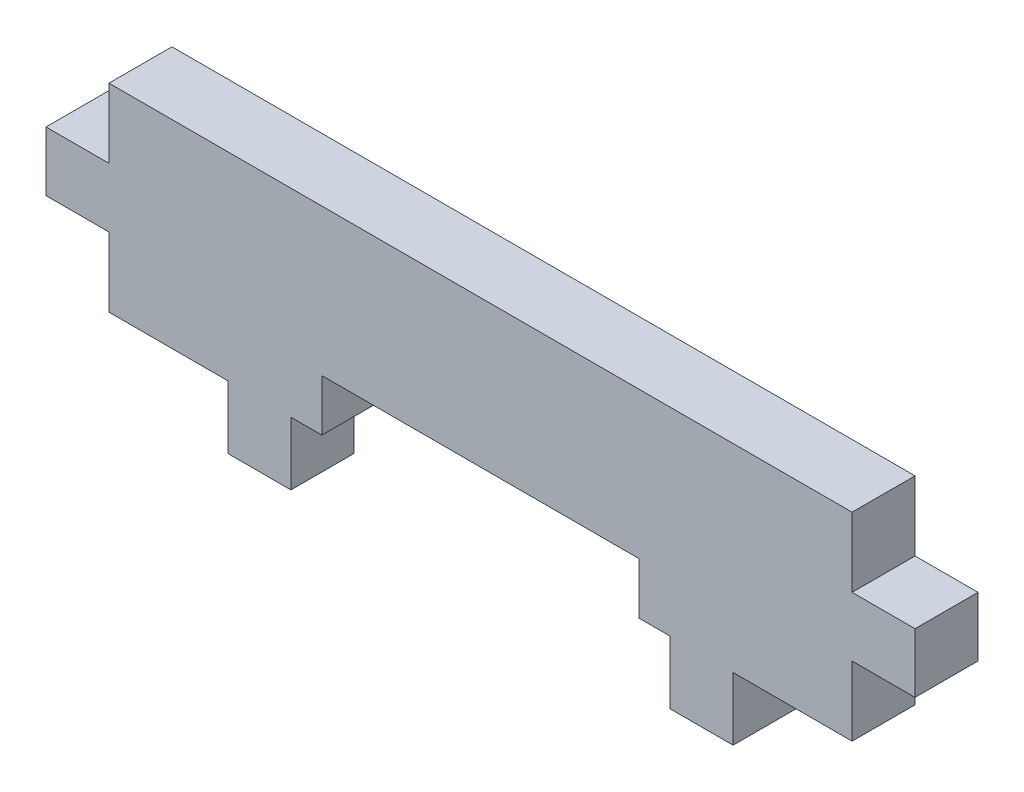
SolidWorks part; units mm, degrees
ref_plane "Front Plane" through (0, 0, 0) normal (0, 0, 1) x (1, 0, 0)
ref_plane "Top Plane" through (0, 0, 0) normal (0, 1, 0) x (1, 0, 0)
ref_plane "Right Plane" through (0, 0, 0) normal (1, 0, 0) x (0, 0, -1)
sketch "Sketch2" plane through (0, 0, 0) normal (0, 0, 1) x (1, 0, 0)
  line L0 (0, 30.3333) -> (0, -1.1776) construction
  line L1 (0, -1.1776) -> (0, -14.8841) construction
  line L2 (12.735, -11.1776) -> (12.735, -14.3526)
  line L3 (12.735, -11.1776) -> (18.735, -11.1776)
  line L4 (18.735, -1.1776) -> (-18.735, -1.1776)
  line L5 (18.735, -11.1776) -> (18.735, -7.6776)
  line L6 (18.735, -7.6776) -> (21.91, -7.6776)
  line L7 (21.91, -4.6776) -> (21.91, -7.6776)
  line L8 (21.91, -4.6776) -> (18.735, -4.6776)
  line L9 (18.735, -4.6776) -> (18.735, -1.1776)
  line L10 (12.735, -14.3526) -> (9.56, -14.3526)
  line L11 (9.56, -14.3526) -> (9.56, -11.1776)
  line L12 (9.56, -11.1776) -> (8, -11.1776)
  line L13 (-8, -8.5776) -> (8, -8.5776)
  line L14 (8, -8.5776) -> (8, -11.1776)
  line L15 (-8, -8.5776) -> (-8, -11.1776)
  line L16 (-9.56, -11.1776) -> (-8, -11.1776)
  line L17 (-9.56, -14.3526) -> (-9.56, -11.1776)
  line L18 (-12.735, -14.3526) -> (-9.56, -14.3526)
  line L19 (-18.735, -4.6776) -> (-18.735, -1.1776)
  line L20 (-21.91, -4.6776) -> (-18.735, -4.6776)
  line L21 (-21.91, -4.6776) -> (-21.91, -7.6776)
  line L22 (-18.735, -7.6776) -> (-21.91, -7.6776)
  line L23 (-18.735, -11.1776) -> (-18.735, -7.6776)
  line L24 (-12.735, -11.1776) -> (-18.735, -11.1776)
  line L25 (-12.735, -11.1776) -> (-12.735, -14.3526)
  point P0 (0, 0)
  point P17 (0, -1.1776)
  point P19 (0, -8.5776)
  point P24 (0, -14.3526)
  dimension "D1" = 3.175
  dimension "D2" = 3.175
  dimension "D3" = 18.735
  dimension "D4" = 3.5
  dimension "D5" = 3
  dimension "D6" = 3.175
  dimension "D7" = 6
  dimension "D8" = 2.6
  dimension "D9" = 8
extrude "Boss-Extrude1" add sketch "Sketch2" against normal blind 3.175
